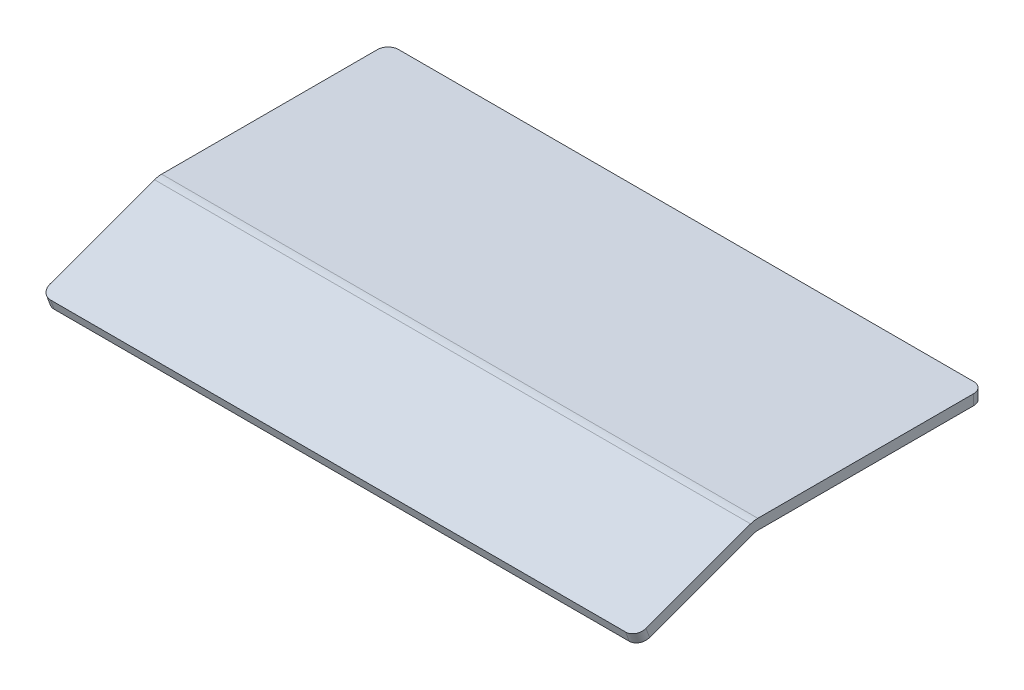
SolidWorks part; units mm, degrees
ref_plane "Front Plane" through (0, 0, 0) normal (0, 0, 1) x (1, 0, 0)
ref_plane "Top Plane" through (0, 0, 0) normal (0, 1, 0) x (1, 0, 0)
ref_plane "Right Plane" through (0, 0, 0) normal (1, 0, 0) x (0, 0, -1)
sketch "Sketch1" plane through (0, 0, 0) normal (1, 0, 0) x (0, 0, -1)
  line L1 (1.1197, 0) -> (138.5803, 0)
  line L3 (-1.1197, 6.35) -> (138.5803, 6.35)
  line L4 (138.5803, 0) -> (138.5803, 6.35)
  line L7 (-1.1197, 6.35) -> (-72.7243, -19.7119)
  line L8 (-72.7243, -19.7119) -> (-70.5524, -25.679)
  line L9 (-70.5524, -25.679) -> (-1.0522, -0.383)
  arc A0 (-1.0522, -0.383) -> (1.1197, 0) centre (1.1197, -6.35) cw
  arc A1 (1.1197, 6.35) -> (-3.224, 5.5841) centre (1.1197, -6.35) ccw
  point P0 (0, 0)
  point P10 (0, 0)
  point P13 (0, 0)
  point P14 (-4.5574, 5.0988)
  point P15 (0, 0)
  point P16 (0, 0)
  dimension "D5" = 6.35
  dimension "D1" = 6.35
  dimension "D2" = 139.7
  dimension "D3" = 160
  dimension "D4" = 76.2
extrude "Boss-Extrude1" add sketch "Sketch1" along normal mid plane 361.95 contours L3 A1 L7 L8 L9 A0 L1 L4
fillet "Fillet1" radius 6.35 4 edges at (180.975, 3.175, -138.5803) (-180.975, 3.175, -138.5803) (-180.975, -22.6955, 71.6383) (180.975, -22.6955, 71.6383)
